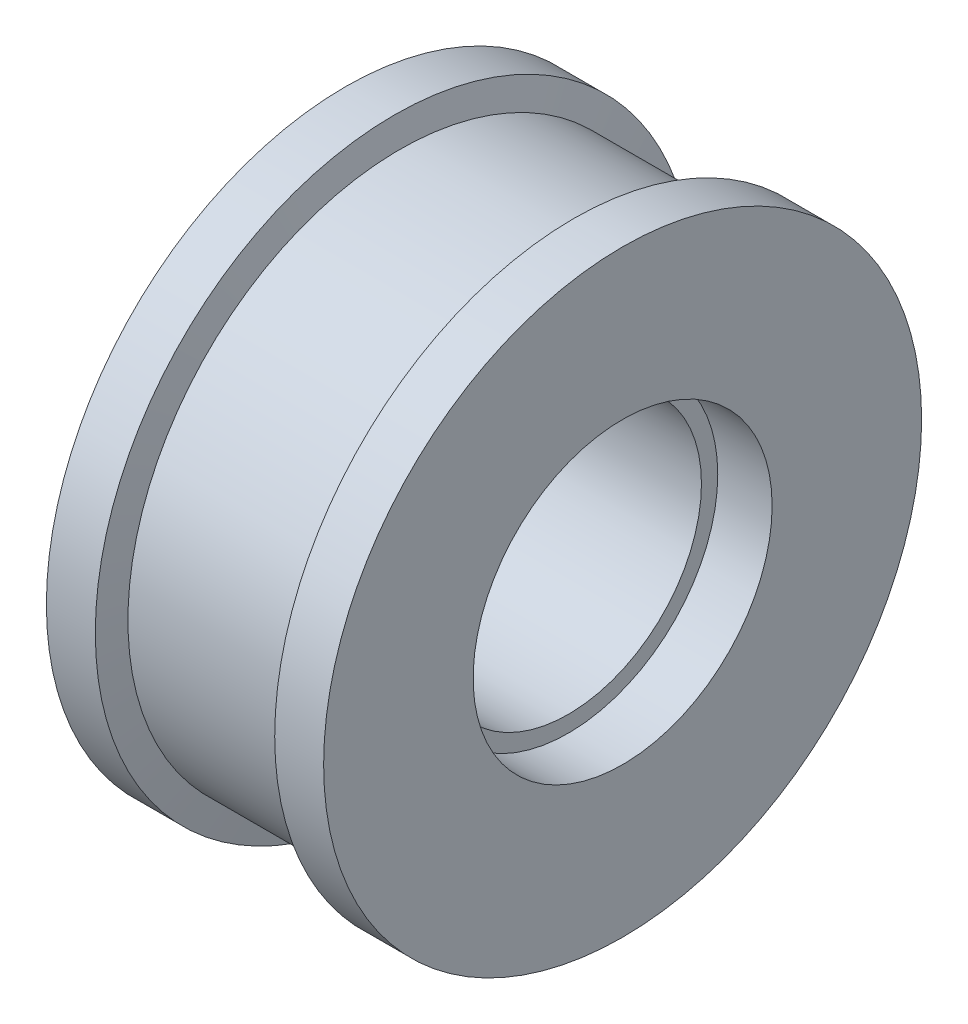
SolidWorks part; units mm, degrees
material "AISI 1045 钢，冷拔"
ref_plane "前视基准面" through (0, 0, 0) normal (0, 0, 1) x (1, 0, 0)
ref_plane "上视基准面" through (0, 0, 0) normal (0, 1, 0) x (1, 0, 0)
ref_plane "右视基准面" through (0, 0, 0) normal (1, 0, 0) x (0, 0, -1)
sketch "草图1" plane through (0, 0, 6531.2227) normal (0, 1, 0) x (-1, 0, 0)
  line L0 (-51, -6531.2227) -> (0, -6531.2227) construction
  line L1 (-9, -6476.2227) -> (-10, -6481.2227)
  line L2 (-51, -6503.7227) -> (-41, -6503.7227)
  line L3 (-41, -6503.7227) -> (-41, -6506.7227)
  line L4 (-41, -6506.7227) -> (-10, -6506.7227)
  line L5 (-10, -6506.7227) -> (-10, -6503.7227)
  line L6 (-10, -6503.7227) -> (0, -6503.7227)
  line L7 (0, -6503.7227) -> (0, -6476.2227)
  line L8 (0, -6476.2227) -> (-9, -6476.2227)
  line L11 (-41, -6481.2227) -> (-42, -6476.2227)
  line L12 (-42, -6476.2227) -> (-51, -6476.2227)
  line L13 (-51, -6476.2227) -> (-51, -6503.7227)
  line L15 (-10, -6481.2227) -> (-41, -6481.2227)
  line L16 (0, -6503.7227) -> (0, -6531.2227) construction
  line L17 (-51, -6503.7227) -> (-51, -6531.2227) construction
  dimension "D2" = 50
  dimension "D3" = 10
  dimension "D4" = 9
  dimension "D5" = 10
  dimension "D6" = 51
  dimension "D7" = 55
  dimension "D8" = 9
  dimension "D9" = 10
  dimension "D10" = 10
  dimension "D11" = 27.5
  dimension "D12" = 27.5
  dimension "D13" = 3
revolve "旋转1" add sketch "草图1" angle 360 about L0
